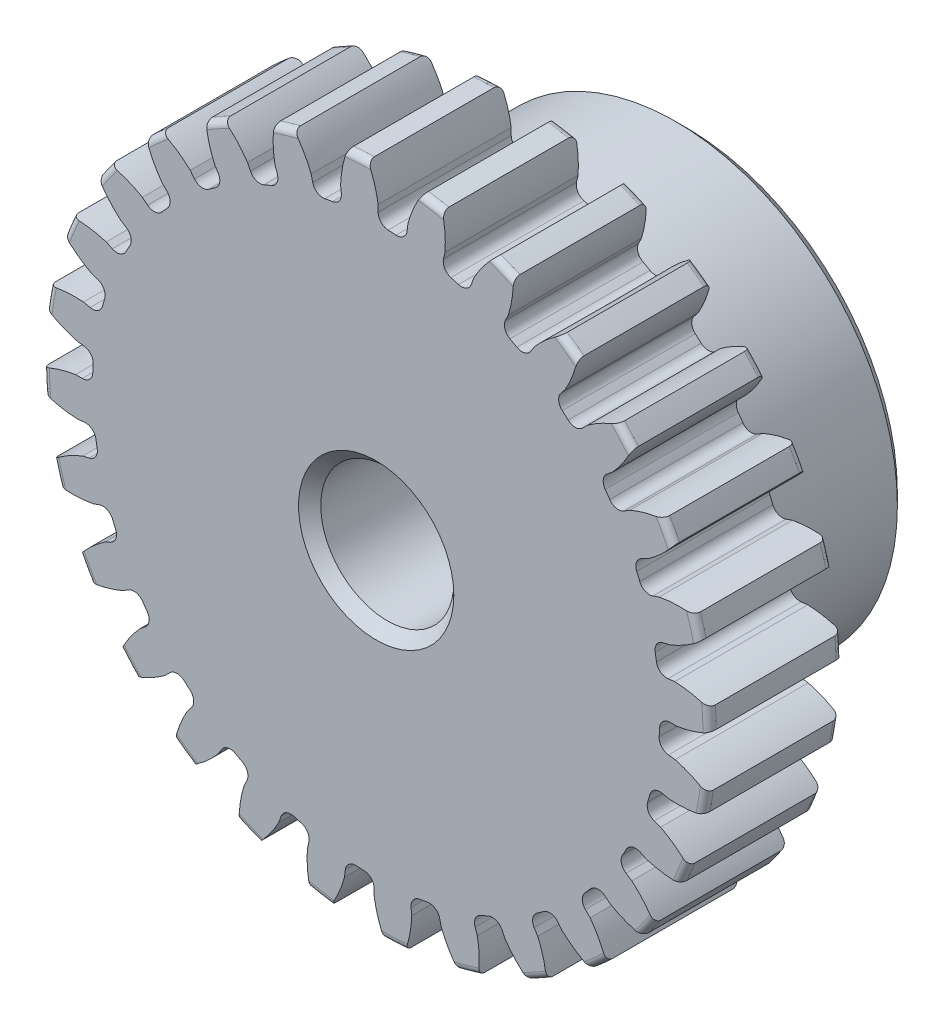
SolidWorks part; units mm, degrees
ref_plane "Front" through (0, 0, 0) normal (0, 0, 1) x (1, 0, 0)
ref_plane "Top" through (0, 0, 0) normal (0, 1, 0) x (1, 0, 0)
ref_plane "Right" through (0, 0, 0) normal (1, 0, 0) x (0, 0, -1)
sketch "Sketch1" plane through (0, 0, 0) normal (0, 0, 1) x (1, 0, 0)
  line L0 (-355.6, 0) -> (355.6, 0) construction
  circle A0 centre (0, 0) radius 11.938
  circle A1 centre (0, 0) radius 11.1125 construction
  circle A3 centre (0, 0) radius 10.1521 construction
  dimension "D1" = 1.7859
  dimension "OD" = 23.876
  dimension "Ptich Dia" = 22.225
  dimension "Root Dia" = 20.3041
  dimension "D3" = 0.8255
  dimension "Number of Teeth" = 711.2
extrude "Boss-Extrude1" add sketch "Sketch1" against normal blind 4.7625
sketch "Sketch2" plane through (0, 0, 0) normal (1, 0, 0) x (0, 0, -1)
  line L0 (4.7625, 0) -> (11.1125, 0)
  line L1 (4.7625, 0) -> (4.7625, 7.9375)
  line L2 (4.7625, 7.9375) -> (11.1125, 7.9375)
  line L3 (11.1125, 7.9375) -> (11.1125, 0)
  point P5 (11.1125, -7.9375)
  point P6 (0, -11.938)
  point P7 (4.7625, -11.938)
  point P9 (0, 11.938)
  dimension "Face Wd" = 4.7625
  dimension "B Hub Dia" = 15.875
  dimension "D O'all Lg." = 11.1125
revolve "Revolve1" add sketch "Sketch2" angle 360 about L0
fillet "Fillet2" radius 0.2388 3 edges at (11.938, 0, -4.7625) (11.938, 0, 0) (7.9375, 0, -4.7625)
sketch "Sketch3" plane through (0, 0, 0) normal (0, 0, 1) x (1, 0, 0)
  line L0 (0, 0) -> (0, 11.938) construction
  line L1 (-2.6937, 10.4159) -> (0, 11.1125)
  line L2 (-9.5921, 11.1125) -> (9.5921, 11.1125) construction
  line L3 (-9.2865, 8.7108) -> (9.2865, 13.5142) construction
  line L4 (-2.6937, 10.4159) -> (0, 0) construction
  line L5 (-6.8708, 8.2788) -> (0, 0) construction
  line L6 (-6.8708, 8.2788) -> (-1.1095, 13.0602) construction
  line L7 (-1.8783, 10.5933) -> (0, 0) construction
  line L8 (-1.8783, 10.5933) -> (0.0394, 10.9333) construction
  arc A0 (-2.6937, 10.4159) -> (-6.8708, 8.2788) centre (0, 0) ccw
  circle A1 centre (0, 0) radius 11.1125 construction
  circle A2 centre (0, 0) radius 10.7585 construction
  arc A3 (-2.6937, 10.4159) -> (-1.8783, 10.5933) centre (0, 0) cw
  circle A4 centre (0, 0) radius 11.938 construction
  point P6 (0, 11.1125)
  dimension "D1" = 2.7823
  dimension "Pressure Angle" = 14.5
  dimension "D2" = 4.73
  dimension "D3" = 7.4869
  dimension "D4" = 0.8347
  dimension "D5" = 1.9476
sketch "Sketch4" plane through (0, 0, 0) normal (0, 0, 1) x (1, 0, 0)
  line L0 (0, 0) -> (0.6221, 11.0776) construction
  line L1 (0.0698, 10.7583) -> (0.0698, 10.1518)
  line L2 (0, 11.1125) -> (1.2442, 11.0426) construction
  line L3 (1.1352, 10.6985) -> (1.0673, 10.0958)
  line L4 (0.0698, 10.1518) -> (0, 0) construction
  line L5 (0, 0) -> (0, 11.938) construction
  line L6 (-6.8708, 8.2788) -> (-1.1095, 13.0602) construction
  line L7 (-6.8708, 8.2788) -> (-1.1095, 13.0602) construction
  arc A0 (1.0673, 10.0958) -> (0.0698, 10.1518) centre (0, 0) ccw
  arc A1 (0, 11.1125) -> (1.2442, 11.0426) centre (0, 0) cw construction
  circle A2 centre (0, 0) radius 11.1125 construction
  circle A3 centre (0, 0) radius 10.7585 construction
  circle A4 centre (0, 0) radius 10.1521 construction
  arc A5 (2.5648, 12.8539) -> (-1.1095, 13.0602) centre (0, 0) ccw
  spline S0 degree 2 poles (-1.1095, 13.0602) (-0.1251, 12.0461) (0.0698, 10.7583) knots 0 0 0 1 1 1
  spline S1 degree 2 poles (2.5648, 12.8539) (1.4731, 11.9563) (1.1352, 10.6985) knots 0 0 0 1 1 1
  dimension "D1" = 1.2468
extrude "Cut-Extrude1" cut sketch "Sketch4" against normal through all
fillet "Fillet1" radius 0.374 2 edges at (1.0673, 10.0958, -2.3813) (0.0698, 10.1518, -2.3813)
pattern_circular "CirPattern1" count 28 over 360 about axis through (0, 0, -4.7625) along (0, 0, 1) of "Cut-Extrude1", "Fillet1"
sketch "Sketch5" plane through (0, 0, 0) normal (0, 0, 1) x (1, 0, 0)
  circle A0 centre (0, 0) radius 2.3813
  dimension "Bore Min" = 4.7625
extrude "Cut-Extrude2" cut sketch "Sketch5" against normal through all
chamfer "Chamfer1" distance 0.3969 angle 45 3 edges at (7.9375, 0, -11.1125) (2.3813, 0, 0) (2.3813, 0, -11.1125)
sketch "Pitch Dia" plane through (0, 0, 0) normal (0, 0, 1) x (1, 0, 0)
  circle A0 centre (0, 0) radius 11.1125 construction
  circle A1 centre (0, 0) radius 11.1125 construction
equation "\"D1@Boss-Extrude1\" = \"Face Wd@Sketch2\""
equation "\"D2@Sketch3\" = \"D1@Sketch3\"*1.7"
equation "\"D3@Sketch3\" = \"D1@Sketch3\"+\"D2@Sketch3\"-.001"
equation "\"D4@Sketch3\" = \"D1@Sketch3\"*.3"
equation "\"D5@Sketch3\" = \"D1@Sketch3\"-\"D4@Sketch3\""
equation "\"D1@Sketch4\" = 1.5708/(\"Number of Teeth@Sketch1\"/\"Ptich Dia@Sketch1\")"
equation "\"D1@Chamfer1\" = \"B Hub Dia@Sketch2\"*.025"
equation "\"D1@CirPattern1\" = \"Number of Teeth@Sketch1\""
equation "\"D1@Fillet1\" = \"D1@Sketch4\"*.3"
equation "\"D1@Fillet2\" = \"OD@Sketch1\"*.01"
equation "\"D1@Sketch1\" = 2.250/(\"Number of Teeth@Sketch1\"/\"Ptich Dia@Sketch1\")"
